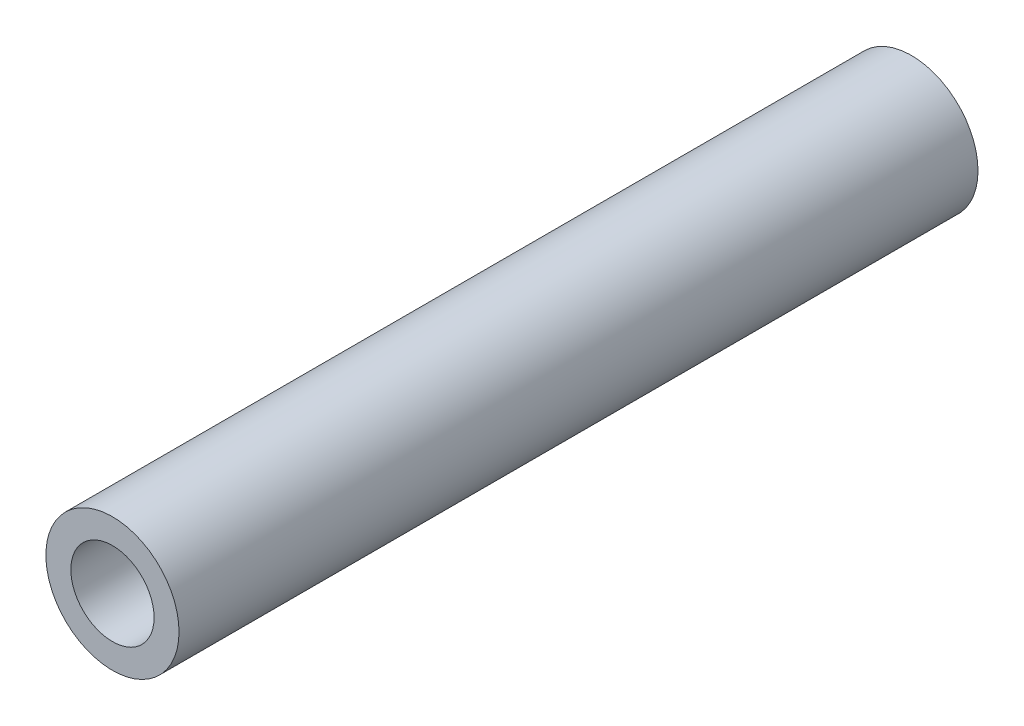
SolidWorks part; units mm, degrees
ref_plane "Front" through (0, 0, 0) normal (0, 0, 1) x (1, 0, 0)
ref_plane "Top" through (0, 0, 0) normal (0, 1, 0) x (1, 0, 0)
ref_plane "Right" through (0, 0, 0) normal (1, 0, 0) x (0, 0, -1)
sketch "草图1" plane through (0, 0, 0) normal (0, 0, 1) x (1, 0, 0)
  circle A0 centre (0, 0) radius 2.5
  circle A1 centre (0, 0) radius 4
extrude "凸台-拉伸1" add sketch "草图1" along normal blind 48
